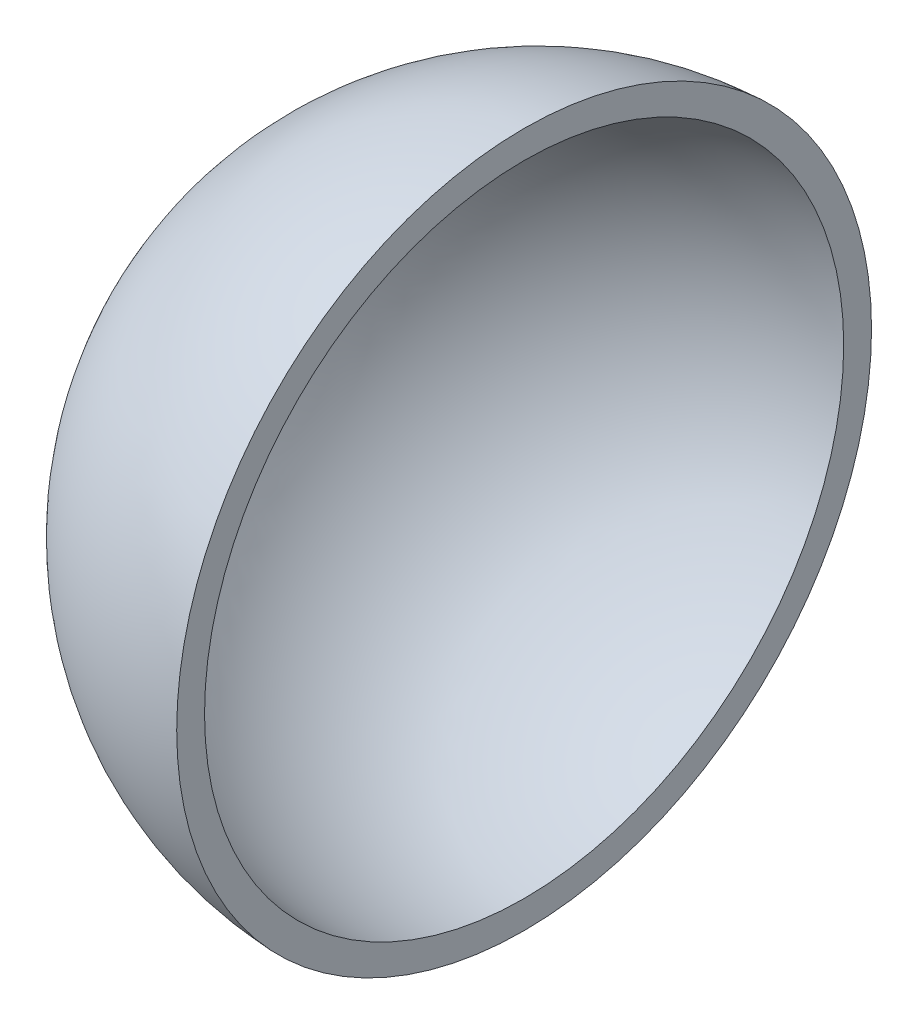
SolidWorks part; units mm, degrees
ref_plane "前视基准面" through (0, 0, 0) normal (0, 0, 1) x (1, 0, 0)
ref_plane "上视基准面" through (0, 0, 0) normal (0, 1, 0) x (1, 0, 0)
ref_plane "右视基准面" through (0, 0, 0) normal (1, 0, 0) x (0, 0, -1)
sketch "草图1" plane through (0, 0, 0) normal (0, 1, 0) x (1, 0, 0)
  line L0 (-25, -20.4768) -> (-25, 22.9187) construction
  line L1 (-1, 17.2675) -> (-1, -17.1978) construction
  line L2 (0, 0) -> (-24.5737, 0) construction
  line L3 (-23, 0) -> (-25, 0)
  line L4 (-1, -22.9783) -> (-1, -24.98)
  arc A0 (-25, 0) -> (-1, -24.98) centre (0, 0) ccw
  arc A1 (-23, 0) -> (-1, -22.9783) centre (0, 0) ccw
  circle A2 centre (0, 0) radius 25 construction
  circle A3 centre (0, 0) radius 23 construction
  dimension "D1" = 50
  dimension "D2" = 24
  dimension "D3" = 2
revolve "旋转1" add sketch "草图1" angle 360 about L2
